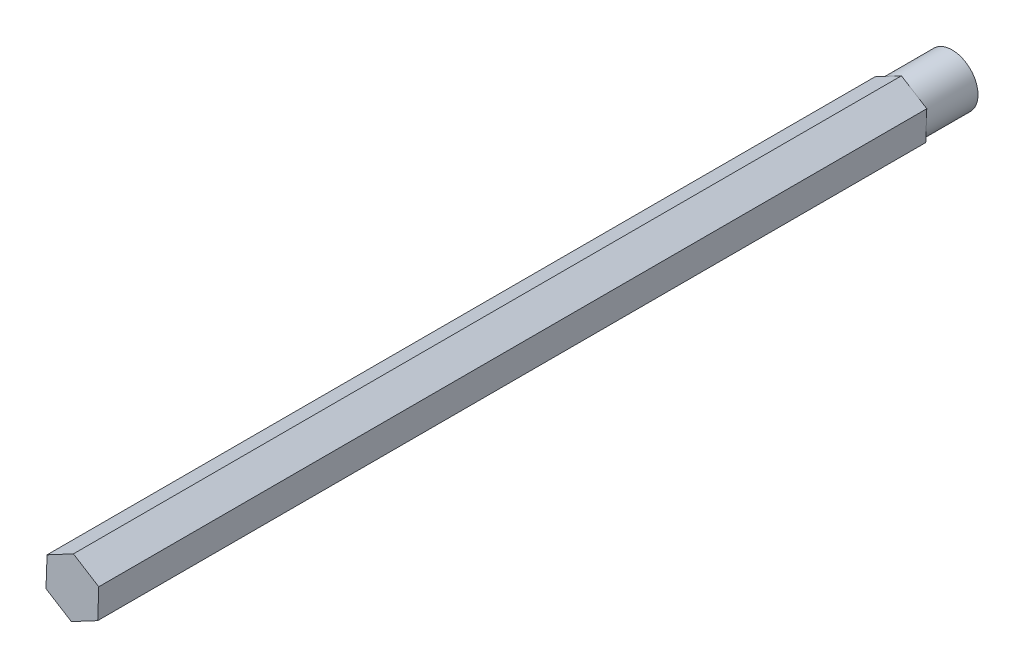
SolidWorks part; units mm, degrees
ref_plane "Front Plane" through (0, 0, 0) normal (0, 0, 1) x (1, 0, 0)
ref_plane "Top Plane" through (0, 0, 0) normal (0, 1, 0) x (1, 0, 0)
ref_plane "Right Plane" through (0, 0, 0) normal (1, 0, 0) x (0, 0, -1)
sketch "Sketch1" plane through (0, 0, 0) normal (0, 0, 1) x (1, 0, 0)
  line L1 (6.2178, -3.8861) -> (6.4744, 3.4417)
  line L2 (6.4744, 3.4417) -> (0.2566, 7.3279)
  line L3 (0.2566, 7.3279) -> (-6.2178, 3.8861)
  line L4 (-6.2178, 3.8861) -> (-6.4744, -3.4417)
  line L5 (-6.4744, -3.4417) -> (-0.2566, -7.3279)
  line L6 (-0.2566, -7.3279) -> (6.2178, -3.8861)
  circle A0 centre (0, 0) radius 6.35 construction
extrude "Boss-Extrude1" add sketch "Sketch1" along normal blind 203.2
sketch "Sketch2" plane through (0, 0, 0) normal (0, 0, -1) x (-1, 0, 0)
  circle A0 centre (0, 0) radius 6.35
extrude "Boss-Extrude2" add sketch "Sketch2" along normal blind 12.7
